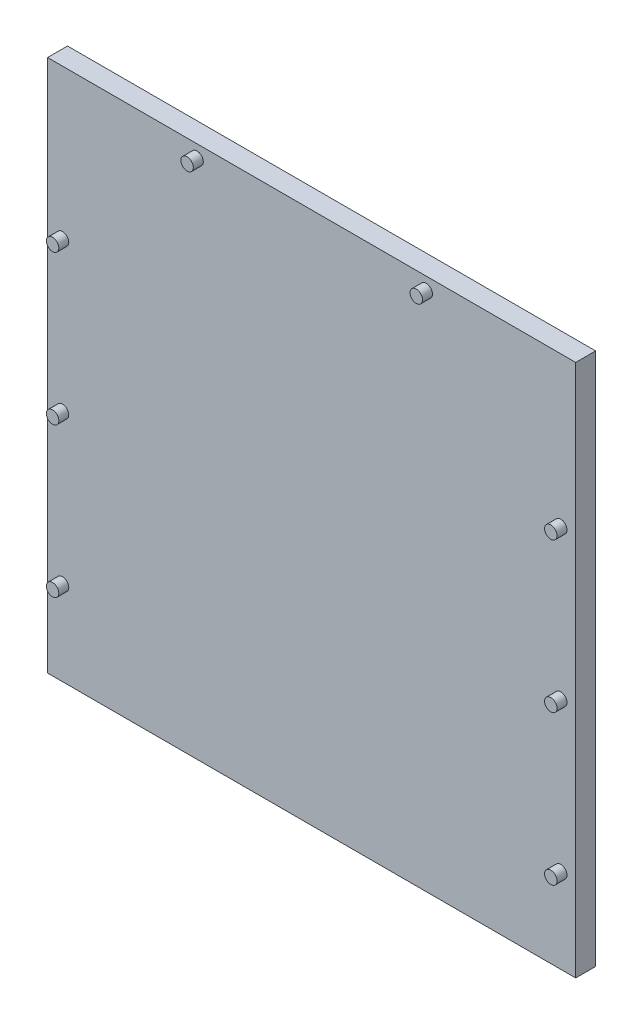
SolidWorks part; units mm, degrees
ref_plane "Front Plane" through (0, 0, 0) normal (0, 0, 1) x (1, 0, 0)
ref_plane "Top Plane" through (0, 0, 0) normal (0, 1, 0) x (1, 0, 0)
ref_plane "Right Plane" through (0, 0, 0) normal (1, 0, 0) x (0, 0, -1)
sketch "Sketch1" plane through (0, 0, 0) normal (0, 0, 1) x (1, 0, 0)
  line L1 (26.5, -26.75) -> (-26.5, -26.75)
  line L2 (26.5, -26.75) -> (26.5, 26.75)
  line L3 (26.5, 26.75) -> (-26.5, 26.75)
  line L4 (-26.5, -26.75) -> (-26.5, 26.75)
  line L5 (26.5, -26.75) -> (-26.5, 26.75) construction
  line L6 (26.5, 26.75) -> (-26.5, -26.75) construction
  point P0 (0, 0)
  dimension "D1" = 53
  dimension "D2" = 53.5
extrude "body" add sketch "Sketch1" along normal blind 2
sketch "Sketch2" plane through (0, 0, 2) normal (0, 0, 1) x (1, 0, 0)
  line L0 (-26.5, 25.5) -> (26.5, 25.5) construction
  line L1 (-26.5, 26.75) -> (-26.5, -26.75) construction
  line L2 (26.5, -26.75) -> (26.5, 26.75) construction
  line L3 (-25, 26.75) -> (-25, -26.75) construction
  line L4 (26.5, 26.75) -> (-26.5, 26.75) construction
  line L5 (-26.5, -26.75) -> (26.5, -26.75) construction
  line L6 (25, 26.75) -> (25, -26.75) construction
  circle A0 centre (-11.5, 25.5) radius 0.625
  circle A1 centre (11.5, 25.5) radius 0.625
  circle A2 centre (-25, 11.75) radius 0.625
  circle A3 centre (-25, -3.25) radius 0.625
  circle A4 centre (-25, -18.25) radius 0.625
  circle A5 centre (25, 11.75) radius 0.625
  circle A6 centre (25, -3.25) radius 0.625
  circle A7 centre (25, -18.25) radius 0.625
  dimension "D12" = 1.25
  dimension "D13" = 1.25
  dimension "D14" = 1.25
  dimension "D15" = 1.25
  dimension "D16" = 1.25
  dimension "D17" = 1.25
  dimension "D18" = 1.25
  dimension "D19" = 1.25
  dimension "D1" = 1.25
  dimension "D2" = 1.5
  dimension "D3" = 1.5
  dimension "D4" = 15
  dimension "D5" = 15
  dimension "D6" = 15
  dimension "D7" = 15
  dimension "D8" = 15
  dimension "D9" = 15
  dimension "D10" = 15
  dimension "D11" = 15
extrude "pins" add sketch "Sketch2" along normal blind 1
